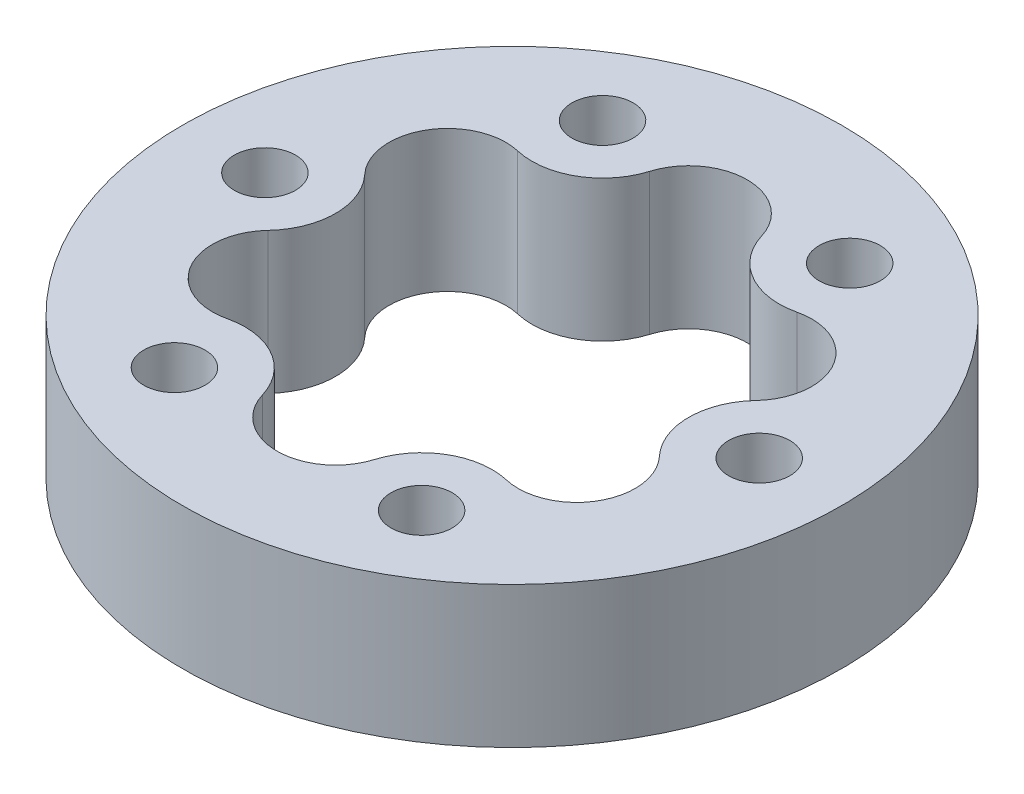
SolidWorks part; units mm, degrees
material "Hexcel AS4C (3000 丝)"
ref_plane "前视基准面" through (0, 0, 0) normal (0, 0, 1) x (1, 0, 0)
ref_plane "上视基准面" through (0, 0, 0) normal (0, 1, 0) x (1, 0, 0)
ref_plane "右视基准面" through (0, 0, 0) normal (1, 0, 0) x (0, 0, -1)
sketch "草图1" plane through (0, 0, 0) normal (0, 1, 0) x (1, 0, 0)
  line L0 (0, 25) -> (0, 0) construction
  line L1 (0, 0) -> (10.5, 18.1865) construction
  circle A0 centre (0, 0) radius 28
  circle A1 centre (0, 0) radius 25 construction
  circle A2 centre (0, 25) radius 1.25 construction
  circle A3 centre (21.6506, 12.5) radius 1.25 construction
  circle A4 centre (21.6506, -12.5) radius 1.25 construction
  circle A5 centre (0, -25) radius 1.25 construction
  circle A6 centre (-21.6506, -12.5) radius 1.25 construction
  circle A7 centre (-21.6506, 12.5) radius 1.25 construction
  circle A8 centre (0, 0) radius 15 construction
  circle A9 centre (0, 15) radius 4 construction
  circle A10 centre (12.9904, -7.5) radius 4 construction
  circle A11 centre (-12.9904, -7.5) radius 4 construction
  circle A12 centre (0, 0) radius 21 construction
  circle A13 centre (10.5, 18.1865) radius 2.6
  circle A14 centre (21, 0) radius 2.6
  circle A15 centre (10.5, -18.1865) radius 2.6
  circle A16 centre (-10.5, -18.1865) radius 2.6
  circle A17 centre (-21, 0) radius 2.6
  circle A18 centre (-10.5, 18.1865) radius 2.6
  dimension "D1" = 2.5
  dimension "D2" = 50
  dimension "D3" = 56
  dimension "D5" = 30
  dimension "D6" = 8
  dimension "D9" = 5.2
  dimension "D10" = 42
  dimension "D8" = 30
  dimension "D4" = 6
  dimension "D7" = 3
  dimension "D11" = 6
extrude "凸台-拉伸1" add sketch "草图1" along normal blind 12
sketch "草图4" plane through (0, 12, 0) normal (0, 1, 0) x (1, 0, 0)
  circle A0 centre (0, 0) radius 15 construction
  circle A1 centre (0, 15) radius 4 construction
  circle A2 centre (12.9904, 7.5) radius 4 construction
  circle A3 centre (12.9904, -7.5) radius 4 construction
  circle A4 centre (0, -15) radius 4 construction
  circle A5 centre (-12.9904, -7.5) radius 4 construction
  circle A6 centre (-12.9904, 7.5) radius 4 construction
  arc A7 (4.7586, 16.4441) -> (11.8617, 12.3431) centre (10.5, 18.1865) ccw
  arc A8 (-4.7586, 16.4441) -> (4.7586, 16.4441) centre (0, 15) cw
  arc A9 (11.8617, 12.3431) -> (16.6203, 4.101) centre (12.9904, 7.5) cw
  arc A10 (16.6203, 4.101) -> (16.6203, -4.101) centre (21, 0) ccw
  arc A11 (16.6203, -4.101) -> (11.8617, -12.3431) centre (12.9904, -7.5) cw
  arc A12 (11.8617, -12.3431) -> (4.7586, -16.4441) centre (10.5, -18.1865) ccw
  arc A13 (4.7586, -16.4441) -> (-4.7586, -16.4441) centre (0, -15) cw
  arc A14 (-4.7586, -16.4441) -> (-11.8617, -12.3431) centre (-10.5, -18.1865) ccw
  arc A15 (-11.8617, -12.3431) -> (-16.6203, -4.101) centre (-12.9904, -7.5) cw
  arc A16 (-16.6203, -4.101) -> (-16.6203, 4.101) centre (-21, 0) ccw
  arc A17 (-16.6203, 4.101) -> (-11.8617, 12.3431) centre (-12.9904, 7.5) cw
  arc A18 (-11.8617, 12.3431) -> (-4.7586, 16.4441) centre (-10.5, 18.1865) ccw
  dimension "D1" = 30
  dimension "D2" = 8
  dimension "D4" = 6
  dimension "D3" = 6
  dimension "D5" = 6
extrude "切除-拉伸2" cut sketch "草图4" against normal through all and the other way through all
move or copy body "实体-移动/复制1" bodies to move or copy 109
